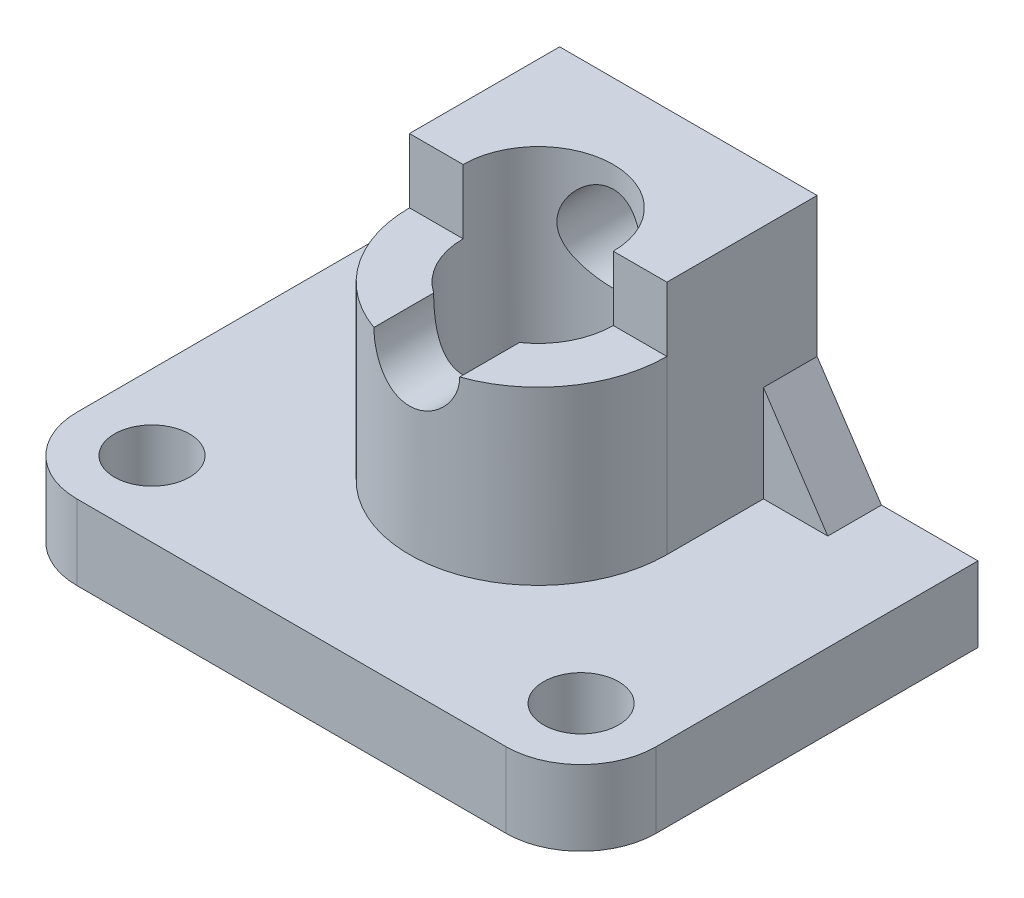
SolidWorks part; units mm, degrees
ref_plane "前视基准面" through (0, 0, 0) normal (0, 0, 1) x (1, 0, 0)
ref_plane "上视基准面" through (0, 0, 0) normal (0, 1, 0) x (1, 0, 0)
ref_plane "右视基准面" through (0, 0, 0) normal (1, 0, 0) x (0, 0, -1)
sketch "草图1" plane through (0, 0, 0) normal (0, 1, 0) x (1, 0, 0)
  line L0 (0, 0) -> (27, 0)
  line L5 (27, 0) -> (27, -37)
  line L6 (27, -37) -> (-27, -37)
  line L7 (-27, -37) -> (-27, 0)
  line L8 (-27, 0) -> (0, 0)
  dimension "D1" = 54
  dimension "D2" = 27
  dimension "D3" = 37
extrude "凸台-拉伸1" add sketch "草图1" along normal blind 7
sketch "草图2" plane through (0, 0, 0) normal (0, 1, 0) x (1, 0, 0)
  line L0 (27, 0) -> (-27, 0) construction
  line L1 (0, 0) -> (0, -38.7793) construction
  circle A0 centre (-20, -30) radius 3.5
  circle A1 centre (20, -30) radius 3.5
  dimension "D1" = 7
  dimension "D2" = 30
  dimension "D3" = 20
extrude "切除-拉伸2" cut sketch "草图2" along normal blind 7
fillet "圆角1" radius 7 2 edges at (27, 3.5, 37) (-27, 3.5, 37)
sketch "草图3" plane through (0, 0, 0) normal (0, 1, 0) x (1, 0, 0)
  line L0 (0, 0) -> (-12, 0)
  line L1 (27, 0) -> (-27, 0) construction
  line L2 (-12, 0) -> (-12, -14)
  line L3 (0, 0) -> (12, 0)
  line L4 (12, 0) -> (12, -14)
  line L6 (0, 0) -> (0, -28.1201) construction
  arc A0 (-12, -14) -> (12, -14) centre (0, -14) ccw
  dimension "D1" = 24
  dimension "D2" = 12
  dimension "D3" = 14
extrude "凸台-拉伸2" add sketch "草图3" along normal blind 29
sketch "草图4" plane through (0, 29, 0) normal (0, 1, 0) x (1, 0, 0)
  circle A0 centre (0, -14) radius 7
  dimension "D1" = 14
extrude "切除-拉伸3" cut sketch "草图4" against normal through all
sketch "草图5" plane through (0, 29, 0) normal (0, 1, 0) x (1, 0, 0)
  line L0 (-7, -14) -> (-12, -14)
  line L1 (0, -15.95) -> (0, 15.95) construction
  line L2 (7, -14) -> (12, -14)
  circle A0 centre (0, -14) radius 7 construction
  arc A1 (-12, -14) -> (12, -14) centre (0, -14) ccw
  arc A2 (-7, -14) -> (7, -14) centre (0, -14) ccw
  arc A3 (-12, -14) -> (12, -14) centre (0, -14) ccw construction
  point P6 (0, 0)
  point P7 (0, 0)
  point P9 (12, -14)
  point P12 (7, -14)
  point P18 (0, 0)
  point P19 (0, 0)
extrude "切除-拉伸4" cut sketch "草图5" against normal blind 6
sketch "草图6" plane through (0, 0, 14) normal (0, 0, 1) x (1, 0, 0)
  line L0 (12, 23) -> (-12, 23) construction
  circle A0 centre (0, 23) radius 4
  dimension "D1" = 8
extrude "切除-拉伸5" cut sketch "草图6" against normal through all and the other way blind 17
sketch "草图8" plane through (0, 0, 0) normal (0, 0, 1) x (1, 0, 0)
  line L0 (-12, 16) -> (-18, 7)
  line L1 (-12, 23) -> (-12, 7) construction
  line L2 (-20, 7) -> (20, 7) construction
  line L3 (-18, 7) -> (-12, 7)
  line L4 (-12, 7) -> (-12, 16)
  line L5 (0, -15.95) -> (0, 15.95) construction
  line L6 (12, 7) -> (12, 16)
  line L7 (18, 7) -> (12, 7)
  line L8 (12, 16) -> (18, 7)
  point P6 (0, 0)
  point P8 (0, 0)
  point P12 (-13.0266, 8.4343)
  dimension "D1" = 18
  dimension "D2" = 9
extrude "凸台-拉伸3" add sketch "草图8" along normal blind 5
